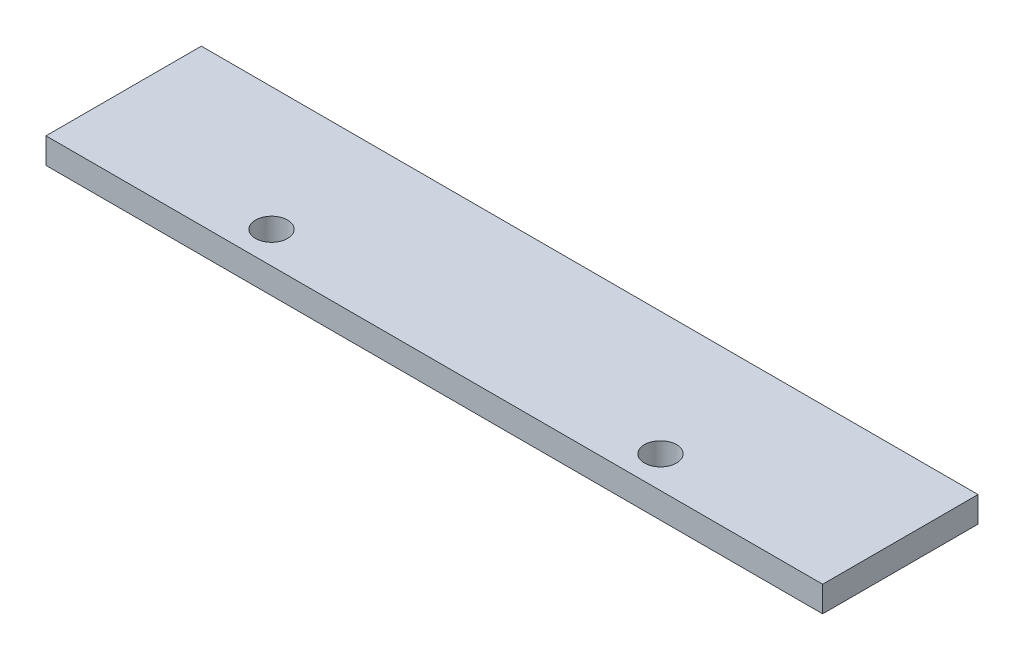
SolidWorks part; units mm, degrees
ref_plane "Front Plane" through (0, 0, 0) normal (0, 0, 1) x (1, 0, 0)
ref_plane "Top Plane" through (0, 0, 0) normal (0, 1, 0) x (1, 0, 0)
ref_plane "Right Plane" through (0, 0, 0) normal (1, 0, 0) x (0, 0, -1)
sketch "Sketch1" plane through (0, 0, 0) normal (0, 1, 0) x (1, 0, 0)
  line L1 (-25.55, -5.11) -> (25.55, -5.11)
  line L2 (-25.55, -5.11) -> (-25.55, 5.11)
  line L3 (-25.55, 5.11) -> (25.55, 5.11)
  line L4 (25.55, -5.11) -> (25.55, 5.11)
  line L5 (-25.55, -5.11) -> (25.55, 5.11) construction
  line L6 (-25.55, 5.11) -> (25.55, -5.11) construction
  point P0 (0, 0)
  dimension "D1" = 51.1
  dimension "D2" = 10.22
extrude "Boss-Extrude1" add sketch "Sketch1" along normal mid plane 1.69
sketch "Sketch2" plane through (0, 0.845, 0) normal (0, 1, 0) x (1, 0, 0)
  circle A0 centre (-12.8065, -3.0157) radius 1.0543
  circle A1 centre (12.786, -3.0157) radius 1.0543
extrude "Cut-Extrude1" cut sketch "Sketch2" against normal through all
